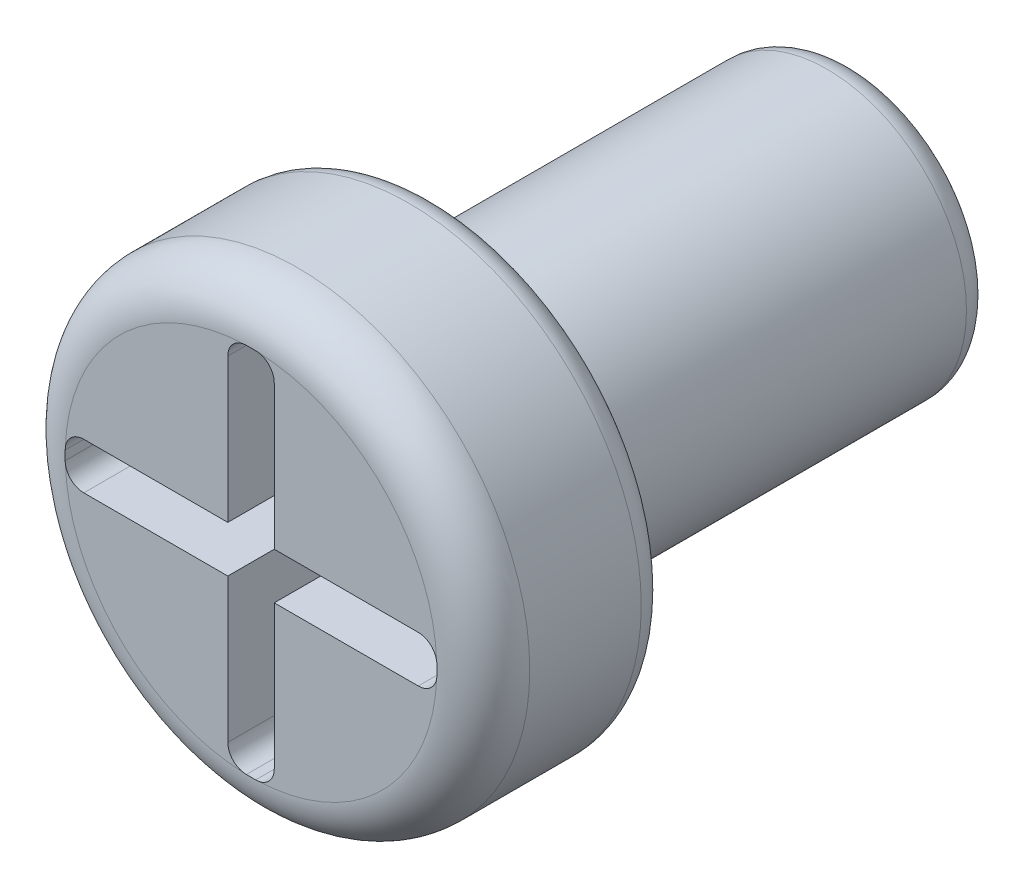
SolidWorks part; units mm, degrees
ref_plane "Ön Düzlem" through (0, 0, 0) normal (0, 0, 1) x (1, 0, 0)
ref_plane "Üst Düzlem" through (0, 0, 0) normal (0, 1, 0) x (1, 0, 0)
ref_plane "Sağ Düzlem" through (0, 0, 0) normal (1, 0, 0) x (0, 0, -1)
sketch "Çizim1" plane through (0, 0, 0) normal (0, 0, 1) x (1, 0, 0)
  circle A0 centre (0, 0) radius 1.5
  dimension "D1" = 3
extrude "Yükseklik-Ekstrüzyon1" add sketch "Çizim1" against normal blind 4.5
sketch "Çizim2" plane through (0, 0, 0) normal (0, 0, 1) x (1, 0, 0)
  circle A0 centre (0, 0) radius 2.5
  dimension "D1" = 5
extrude "Yükseklik-Ekstrüzyon2" add sketch "Çizim2" along normal blind 2
fillet "Radyus1" radius 0.5 1 edges at (2.5, 0, 2)
fillet "Radyus2" radius 0.3 2 edges at (1.5, 0, -4.5) (2.5, 0, 0)
sketch "Çizim3" plane through (0, 0, 2) normal (0, 0, 1) x (1, 0, 0)
  line L1 (-0.05, 2) -> (0.05, 2)
  line L2 (-0.25, 1.8) -> (-0.25, 0.25)
  line L3 (-0.05, -2) -> (0.05, -2)
  line L4 (0.25, 1.8) -> (0.25, 0.25)
  line L7 (-1.8, 0.25) -> (-0.25, 0.25)
  line L8 (-2, 0.05) -> (-2, -0.05)
  line L9 (-1.8, -0.25) -> (-0.25, -0.25)
  line L10 (2, 0.05) -> (2, -0.05)
  line L15 (0.25, 0.25) -> (1.8, 0.25)
  line L17 (0.25, -0.25) -> (0.25, -1.8)
  line L18 (-0.25, -0.25) -> (-0.25, -1.8)
  line L20 (0.25, -0.25) -> (1.8, -0.25)
  arc A0 (-0.25, -1.8) -> (-0.05, -2) centre (-0.05, -1.8) ccw
  arc A1 (0.05, -2) -> (0.25, -1.8) centre (0.05, -1.8) ccw
  arc A2 (1.8, -0.25) -> (2, -0.05) centre (1.8, -0.05) ccw
  arc A3 (1.8, 0.25) -> (2, 0.05) centre (1.8, 0.05) cw
  arc A4 (0.05, 2) -> (0.25, 1.8) centre (0.05, 1.8) cw
  arc A5 (-0.05, 2) -> (-0.25, 1.8) centre (-0.05, 1.8) ccw
  arc A6 (-2, -0.05) -> (-1.8, -0.25) centre (-1.8, -0.05) ccw
  arc A7 (-1.8, 0.25) -> (-2, 0.05) centre (-1.8, 0.05) ccw
  point P0 (0, 0)
  point P6 (0, 0)
  point P17 (0.25, -2)
  point P22 (2, -0.25)
  point P25 (2, 0.25)
  point P28 (0.25, 2)
  point P31 (-0.25, 2)
  point P34 (-2, -0.25)
  dimension "D5" = 0.2
  dimension "D1" = 4
  dimension "D2" = 0.5
  dimension "D3" = 0.5
  dimension "D4" = 4
extrude "Kes-Ekstrüzyon1" cut sketch "Çizim3" against normal blind 1.5
